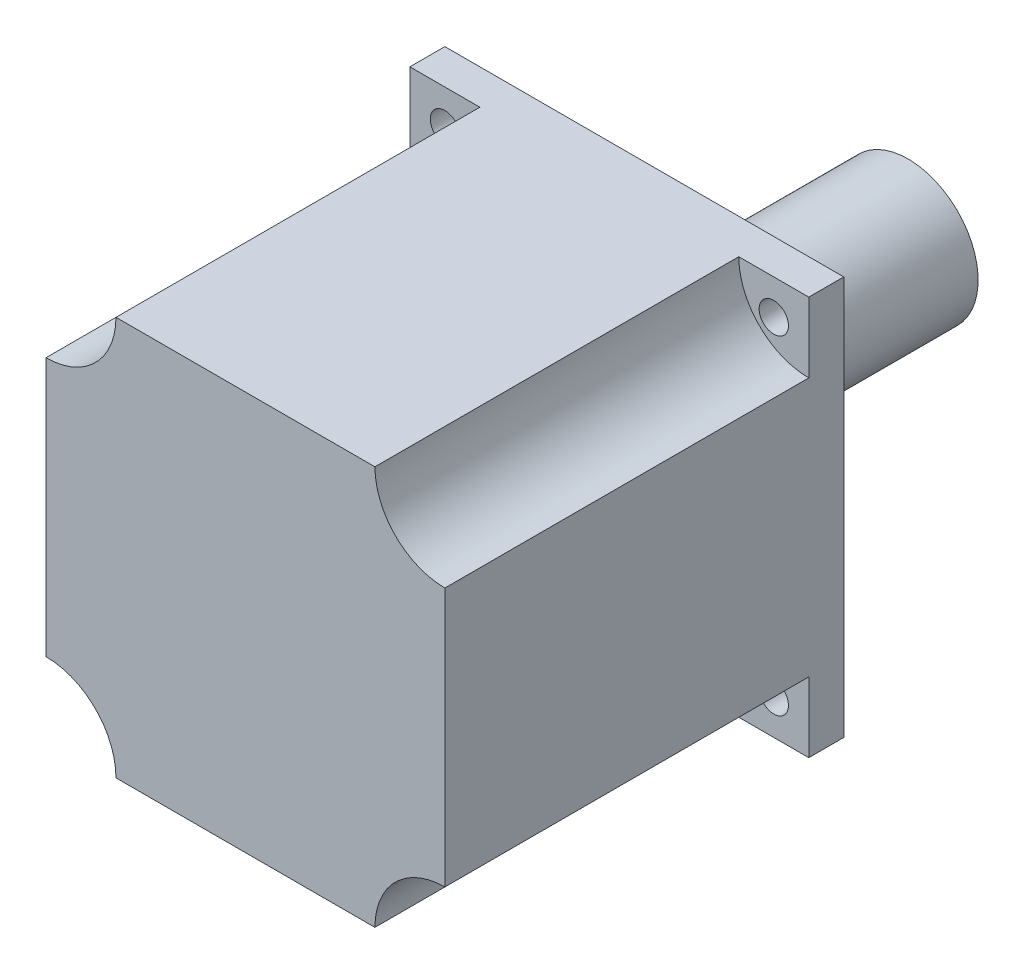
SolidWorks part; units mm, degrees
ref_plane "前视基准面" through (0, 0, 0) normal (0, 0, 1) x (1, 0, 0)
ref_plane "上视基准面" through (0, 0, 0) normal (0, 1, 0) x (1, 0, 0)
ref_plane "右视基准面" through (0, 0, 0) normal (1, 0, 0) x (0, 0, -1)
sketch "草图1" plane through (0, 0, 0) normal (0, 0, 1) x (1, 0, 0)
  line L1 (-28.5, -28.5) -> (28.5, -28.5)
  line L2 (-28.5, -28.5) -> (-28.5, 28.5)
  line L3 (-28.5, 28.5) -> (28.5, 28.5)
  line L4 (28.5, -28.5) -> (28.5, 28.5)
  line L5 (-28.5, -28.5) -> (28.5, 28.5) construction
  line L6 (-28.5, 28.5) -> (28.5, -28.5) construction
  point P0 (0, 0)
  dimension "D1" = 57
  dimension "D2" = 57
extrude "凸台-拉伸1" add sketch "草图1" along normal blind 57
sketch "草图2" plane through (0, 0, 57) normal (0, 0, 1) x (1, 0, 0)
  circle A0 centre (28.5, 28.5) radius 10
  circle A1 centre (-28.5, 28.5) radius 10
  circle A3 centre (28.5, -28.5) radius 10
  circle A4 centre (-28.5, -28.5) radius 10
  dimension "D1" = 20
  dimension "D2" = 20
  dimension "D3" = 20
  dimension "D4" = 20
extrude "切除-拉伸1" cut sketch "草图2" against normal blind 52
sketch "草图3" plane through (0, 0, 5) normal (0, 0, 1) x (1, 0, 0)
  line L7 (-23.5, -23.5) -> (23.5, -23.5) construction
  line L8 (-23.5, -23.5) -> (-23.5, 23.5) construction
  line L9 (-23.5, 23.5) -> (23.5, 23.5) construction
  line L10 (23.5, -23.5) -> (23.5, 23.5) construction
  line L11 (-23.5, -23.5) -> (23.5, 23.5) construction
  line L12 (-23.5, 23.5) -> (23.5, -23.5) construction
  circle A0 centre (23.5, -23.5) radius 2.0941
  circle A2 centre (-23.5, -23.5) radius 2.0941
  circle A3 centre (-23.5, 23.5) radius 2.0941
  circle A4 centre (23.5, 23.5) radius 2.0941
  point P19 (0, 0)
  dimension "D5" = 47
  dimension "D6" = 47
  dimension "D3" = 4
extrude "切除-拉伸3" cut sketch "草图3" against normal through all
sketch "草图4" plane through (0, 0, 0) normal (0, 0, -1) x (-1, 0, 0)
  circle A0 centre (0, 0) radius 5
extrude "凸台-拉伸3" add sketch "草图4" along normal blind 11.7 contours A0
sketch "草图5" plane through (0, 0, -11.7) normal (0, 0, -1) x (-1, 0, 0)
  circle A0 centre (0, 0) radius 10
extrude "凸台-拉伸4" add sketch "草图5" along normal blind 26
